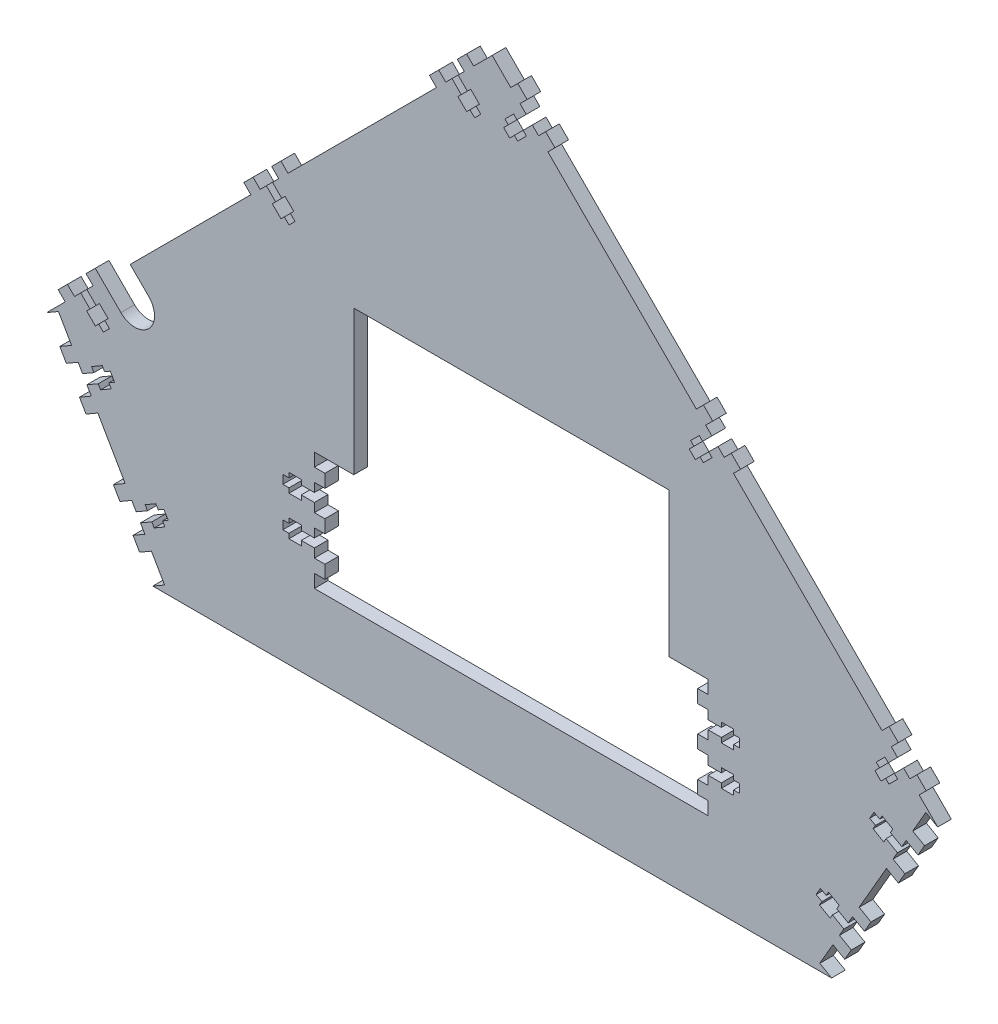
SolidWorks part; units mm, degrees
material "Acrylic (Blue)"
ref_plane "Front Plane" through (0, 0, 0) normal (0, 0, 1) x (1, 0, 0)
ref_plane "Top Plane" through (0, 0, 0) normal (0, 1, 0) x (1, 0, 0)
ref_plane "Right Plane" through (0, 0, 0) normal (1, 0, 0) x (0, 0, -1)
sketch "Sketch1" plane through (0, 0, 0) normal (0, 0, 1) x (1, 0, 0)
  line L0 (0, 0) -> (0, 304.4261) construction
  line L1 (0, 304.4261) -> (215.5261, 88.9)
  line L2 (215.5261, 88.9) -> (164.1997, 0)
  line L3 (164.1997, 0) -> (0, 0)
  line L4 (0, 304.4261) -> (-215.5261, 88.9)
  line L5 (-215.5261, 88.9) -> (-164.1997, 0)
  line L6 (-164.1997, 0) -> (0, 0)
  line L7 (-215.5261, 88.9) -> (215.5261, 88.9) construction
  line L8 (0, 304.4261) -> (3.5921, 308.0182) construction
  line L9 (3.5921, 308.0182) -> (219.1182, 92.4921) construction
  line L10 (219.1182, 92.4921) -> (215.5261, 88.9) construction
  line L11 (3.5921, 308.0182) -> (0, 311.6104) construction
  line L12 (0, 311.6104) -> (-219.1182, 92.4921) construction
  line L13 (-219.1182, 92.4921) -> (-215.5261, 88.9) construction
  line L14 (215.5261, 88.9) -> (219.9256, 86.36) construction
  line L15 (219.9256, 86.36) -> (168.5991, -2.54) construction
  line L16 (168.5991, -2.54) -> (164.1997, 0) construction
  line L17 (164.1997, 0) -> (164.1997, -12.7) construction
  line L18 (164.1997, -12.7) -> (-164.1997, -12.7) construction
  line L19 (-164.1997, -12.7) -> (-164.1997, 0) construction
  line L20 (-164.1997, 0) -> (-168.5991, -2.54) construction
  line L21 (-168.5991, -2.54) -> (-219.9256, 86.36) construction
  line L22 (-219.9256, 86.36) -> (-215.5261, 88.9) construction
  dimension "D1" = 304.8
  dimension "D2" = 120
  dimension "D3" = 88.9
  dimension "D4" = 5.08
  dimension "D5" = 12.7
extrude "Boss-Extrude1" add sketch "Sketch1" along normal blind 6.604
sketch "Sketch2" plane through (0, 0, 6.604) normal (0, 0, 1) x (1, 0, 0)
  line L0 (215.5261, 88.9) -> (0, 304.4261) construction
  line L1 (-66.9554, 165.1) -> (85.4446, 165.1)
  line L2 (-66.9554, 38.1) -> (85.4446, 38.1)
  line L3 (85.4446, 165.1) -> (85.4446, 95.25)
  line L4 (-66.9554, 165.1) -> (-66.9554, 95.25)
  line L6 (-164.1997, 0) -> (164.1997, 0) construction
  line L7 (-66.9554, 38.1) -> (-86.0054, 38.1)
  line L9 (-66.9554, 95.25) -> (-86.0054, 95.25)
  line L10 (-86.0054, 38.1) -> (-86.0054, 95.25)
  line L11 (85.4446, 38.1) -> (104.4946, 38.1)
  line L13 (85.4446, 95.25) -> (104.4946, 95.25)
  line L14 (104.4946, 38.1) -> (104.4946, 95.25)
  dimension "D1" = 127
  dimension "D2" = 38.1
  dimension "D3" = 38.1
  dimension "D4" = 152.4
  dimension "D5" = 19.05
  dimension "D6" = 57.15
extrude "Cut-Extrude1" cut sketch "Sketch2" against normal through all
sketch "Sketch3" plane through (0, 0, 6.604) normal (0, 0, 1) x (1, 0, 0)
  line L0 (-209.8069, 92.202) -> (-215.5261, 88.9)
  line L1 (-215.5261, 88.9) -> (-164.1997, 0)
  line L2 (-164.1997, 0) -> (-158.4805, 3.302)
  line L3 (-158.4805, 3.302) -> (-209.8069, 92.202)
  line L4 (0, 304.4261) -> (0, 0) construction
  line L5 (158.4805, 3.302) -> (209.8069, 92.202)
  line L6 (164.1997, 0) -> (158.4805, 3.302)
  line L7 (215.5261, 88.9) -> (164.1997, 0)
  line L8 (209.8069, 92.202) -> (215.5261, 88.9)
  dimension "D1" = 6.604
extrude "Cut-Extrude2" cut sketch "Sketch3" against normal through all
sketch "Sketch4" plane through (0, 0, 6.604) normal (0, 0, 1) x (1, 0, 0)
  line L0 (0, 304.4261) -> (-215.5261, 88.9) construction
  line L1 (-30.3533, 280.8979) -> (-102.1953, 209.0558) construction
  line L3 (-120.1558, 191.0953) -> (-191.9979, 119.2533) construction
  line L4 (215.5261, 88.9) -> (0, 304.4261) construction
  line L5 (120.1558, 191.0953) -> (191.9979, 119.2533) construction
  line L6 (30.3533, 280.8979) -> (102.1953, 209.0558) construction
  line L7 (215.5261, 88.9) -> (209.8069, 92.202) construction
  line L8 (-158.4805, 3.302) -> (-209.8069, 92.202) construction
  line L9 (-209.8069, 92.202) -> (-215.5261, 88.9) construction
  line L11 (158.4805, 3.302) -> (164.1997, 0) construction
  line L13 (-164.1997, 0) -> (-158.4805, 3.302) construction
  line L14 (209.8069, 92.202) -> (158.4805, 3.302) construction
  line L15 (104.4946, 38.1) -> (104.4946, 95.25) construction
  line L16 (-86.0054, 95.25) -> (-86.0054, 38.1) construction
  line L17 (104.4946, 95.25) -> (85.4446, 95.25) construction
  line B0 (-19.4333, 284.9929) -> (-14.9431, 280.5027) construction
  line B1 (-14.9431, 280.5027) -> (-16.5596, 278.8863) construction
  line B2 (-16.5596, 278.8863) -> (-12.3568, 274.6835) construction
  line B3 (-12.3568, 274.6835) -> (-10.7404, 276.3) construction
  line B4 (-10.7404, 276.3) -> (-8.4774, 274.037) construction
  line B5 (-8.4774, 274.037) -> (-5.5318, 276.9825) construction
  line B6 (-5.5318, 276.9825) -> (-7.7949, 279.2455) construction
  line B7 (-7.7949, 279.2455) -> (-6.1784, 280.862) construction
  line B8 (-6.1784, 280.862) -> (-10.3812, 285.0647) construction
  line B9 (-10.3812, 285.0647) -> (-11.9976, 283.4483) construction
  line B10 (-11.9976, 283.4483) -> (-16.4878, 287.9384) construction
  line B11 (-13.4704, 290.9558) -> (-16.8829, 294.3683) construction
  line B12 (-16.8829, 294.3683) -> (-12.3928, 298.8584) construction
  line B13 (-12.3928, 298.8584) -> (-8.9803, 295.4459) construction
  line B14 (-19.4333, 284.9929) -> (-22.4506, 281.9755) construction
  line B15 (-22.4506, 281.9755) -> (-25.8631, 285.388) construction
  line B16 (-25.8631, 285.388) -> (-30.3533, 280.8979) construction
  line B17 (-30.3533, 280.8979) -> (-26.9408, 277.4854) construction
  line B18 (-16.4878, 287.9384) -> (-19.4333, 284.9929) construction
  line B19 (-109.2358, 195.1903) -> (-104.7457, 190.7002) construction
  line B20 (-104.7457, 190.7002) -> (-106.3622, 189.0837) construction
  line B21 (-106.3622, 189.0837) -> (-102.1594, 184.881) construction
  line B22 (-102.1594, 184.881) -> (-100.5429, 186.4974) construction
  line B23 (-100.5429, 186.4974) -> (-98.2799, 184.2344) construction
  line B24 (-98.2799, 184.2344) -> (-95.3344, 187.1799) construction
  line B25 (-95.3344, 187.1799) -> (-97.5974, 189.4429) construction
  line B26 (-97.5974, 189.4429) -> (-95.981, 191.0594) construction
  line B27 (-95.981, 191.0594) -> (-100.1837, 195.2622) construction
  line B28 (-100.1837, 195.2622) -> (-101.8002, 193.6457) construction
  line B29 (-101.8002, 193.6457) -> (-106.2903, 198.1358) construction
  line B30 (-103.2729, 201.1532) -> (-106.6854, 204.5657) construction
  line B31 (-106.6854, 204.5657) -> (-102.1953, 209.0558) construction
  line B32 (-102.1953, 209.0558) -> (-98.7828, 205.6433) construction
  line B33 (-112.2532, 192.1729) -> (-115.6657, 195.5854) construction
  line B34 (-115.6657, 195.5854) -> (-120.1558, 191.0953) construction
  line B35 (-120.1558, 191.0953) -> (-116.7433, 187.6828) construction
  line B36 (-106.2903, 198.1358) -> (-109.2358, 195.1903) construction
  line B37 (-199.0384, 105.3878) -> (-194.5483, 100.8976) construction
  line B38 (-194.5483, 100.8976) -> (-196.1647, 99.2812) construction
  line B39 (-196.1647, 99.2812) -> (-191.962, 95.0784) construction
  line B40 (-191.962, 95.0784) -> (-190.3455, 96.6949) construction
  line B41 (-190.3455, 96.6949) -> (-188.0825, 94.4318) construction
  line B42 (-188.0825, 94.4318) -> (-185.137, 97.3774) construction
  line B43 (-185.137, 97.3774) -> (-187.4, 99.6404) construction
  line B44 (-187.4, 99.6404) -> (-185.7835, 101.2568) construction
  line B45 (-185.7835, 101.2568) -> (-189.9863, 105.4596) construction
  line B46 (-189.9863, 105.4596) -> (-191.6027, 103.8431) construction
  line B47 (-191.6027, 103.8431) -> (-196.0929, 108.3333) construction
  line B48 (-196.0929, 108.3333) -> (-193.0755, 111.3506) construction
  line B49 (-193.0755, 111.3506) -> (-196.488, 114.7631) construction
  line B50 (-196.488, 114.7631) -> (-191.9979, 119.2533) construction
  line B51 (-191.9979, 119.2533) -> (-188.5854, 115.8408) construction
  line B52 (-199.0384, 105.3878) -> (-202.0558, 102.3704) construction
  line B53 (-202.0558, 102.3704) -> (-205.4683, 105.7829) construction
  line B54 (-205.4683, 105.7829) -> (-209.9584, 101.2928) construction
  line B55 (-209.9584, 101.2928) -> (-206.5459, 97.8803) construction
  line B56 (-196.0929, 108.3333) -> (-199.0384, 105.3878) construction
  line B57 (16.4878, 287.9384) -> (11.9976, 283.4483) construction
  line B58 (11.9976, 283.4483) -> (10.3812, 285.0647) construction
  line B59 (10.3812, 285.0647) -> (6.1784, 280.862) construction
  line B60 (6.1784, 280.862) -> (7.7949, 279.2455) construction
  line B61 (7.7949, 279.2455) -> (5.5318, 276.9825) construction
  line B62 (5.5318, 276.9825) -> (8.4774, 274.037) construction
  line B63 (8.4774, 274.037) -> (10.7404, 276.3) construction
  line B64 (10.7404, 276.3) -> (12.3568, 274.6835) construction
  line B65 (12.3568, 274.6835) -> (16.5596, 278.8863) construction
  line B66 (16.5596, 278.8863) -> (14.9431, 280.5027) construction
  line B67 (14.9431, 280.5027) -> (19.4333, 284.9929) construction
  line B68 (19.4333, 284.9929) -> (22.4506, 281.9755) construction
  line B69 (22.4506, 281.9755) -> (25.8631, 285.388) construction
  line B70 (25.8631, 285.388) -> (30.3533, 280.8979) construction
  line B71 (30.3533, 280.8979) -> (26.9408, 277.4854) construction
  line B72 (16.4878, 287.9384) -> (13.4704, 290.9558) construction
  line B73 (13.4704, 290.9558) -> (16.8829, 294.3683) construction
  line B74 (16.8829, 294.3683) -> (12.3928, 298.8584) construction
  line B75 (12.3928, 298.8584) -> (8.9803, 295.4459) construction
  line B76 (19.4333, 284.9929) -> (16.4878, 287.9384) construction
  line B77 (106.2903, 198.1358) -> (101.8002, 193.6457) construction
  line B78 (101.8002, 193.6457) -> (100.1837, 195.2622) construction
  line B79 (100.1837, 195.2622) -> (95.981, 191.0594) construction
  line B80 (95.981, 191.0594) -> (97.5974, 189.4429) construction
  line B81 (97.5974, 189.4429) -> (95.3344, 187.1799) construction
  line B82 (95.3344, 187.1799) -> (98.2799, 184.2344) construction
  line B83 (98.2799, 184.2344) -> (100.5429, 186.4974) construction
  line B84 (100.5429, 186.4974) -> (102.1594, 184.881) construction
  line B85 (102.1594, 184.881) -> (106.3622, 189.0837) construction
  line B86 (106.3622, 189.0837) -> (104.7457, 190.7002) construction
  line B87 (104.7457, 190.7002) -> (109.2358, 195.1903) construction
  line B88 (109.2358, 195.1903) -> (112.2532, 192.1729) construction
  line B89 (112.2532, 192.1729) -> (115.6657, 195.5854) construction
  line B90 (115.6657, 195.5854) -> (120.1558, 191.0953) construction
  line B91 (120.1558, 191.0953) -> (116.7433, 187.6828) construction
  line B92 (106.2903, 198.1358) -> (103.2729, 201.1532) construction
  line B93 (103.2729, 201.1532) -> (106.6854, 204.5657) construction
  line B94 (106.6854, 204.5657) -> (102.1953, 209.0558) construction
  line B95 (102.1953, 209.0558) -> (98.7828, 205.6433) construction
  line B96 (109.2358, 195.1903) -> (106.2903, 198.1358) construction
  line B97 (196.0929, 108.3333) -> (191.6027, 103.8431) construction
  line B98 (191.6027, 103.8431) -> (189.9863, 105.4596) construction
  line B99 (189.9863, 105.4596) -> (185.7835, 101.2568) construction
  line B100 (185.7835, 101.2568) -> (187.4, 99.6404) construction
  line B101 (187.4, 99.6404) -> (185.137, 97.3774) construction
  line B102 (185.137, 97.3774) -> (188.0825, 94.4318) construction
  line B103 (188.0825, 94.4318) -> (190.3455, 96.6949) construction
  line B104 (190.3455, 96.6949) -> (191.962, 95.0784) construction
  line B105 (191.962, 95.0784) -> (196.1647, 99.2812) construction
  line B106 (196.1647, 99.2812) -> (194.5483, 100.8976) construction
  line B107 (194.5483, 100.8976) -> (199.0384, 105.3878) construction
  line B108 (199.0384, 105.3878) -> (202.0558, 102.3704) construction
  line B109 (202.0558, 102.3704) -> (205.4683, 105.7829) construction
  line B110 (205.4683, 105.7829) -> (209.9584, 101.2928) construction
  line B111 (209.9584, 101.2928) -> (206.5459, 97.8803) construction
  line B112 (193.0755, 111.3506) -> (196.488, 114.7631) construction
  line B113 (196.488, 114.7631) -> (191.9979, 119.2533) construction
  line B114 (191.9979, 119.2533) -> (188.5854, 115.8408) construction
  line B115 (199.0384, 105.3878) -> (196.0929, 108.3333) construction
  line B116 (198.1483, 72.0087) -> (192.6491, 75.1837) construction
  line B117 (192.6491, 75.1837) -> (193.7921, 77.1634) construction
  line B118 (193.7921, 77.1634) -> (188.6447, 80.1352) construction
  line B119 (188.6447, 80.1352) -> (187.5017, 78.1555) construction
  line B120 (187.5017, 78.1555) -> (184.7301, 79.7557) construction
  line B121 (184.7301, 79.7557) -> (182.6473, 76.1482) construction
  line B122 (182.6473, 76.1482) -> (185.4189, 74.548) construction
  line B123 (185.4189, 74.548) -> (184.2759, 72.5683) construction
  line B124 (184.2759, 72.5683) -> (189.4233, 69.5965) construction
  line B125 (189.4233, 69.5965) -> (190.5663, 71.5762) construction
  line B126 (190.5663, 71.5762) -> (196.0655, 68.4012) construction
  line B127 (196.0655, 68.4012) -> (193.9319, 64.7057) construction
  line B128 (193.9319, 64.7057) -> (198.1114, 62.2927) construction
  line B129 (198.1114, 62.2927) -> (194.9364, 56.7934) construction
  line B130 (194.9364, 56.7934) -> (190.7569, 59.2064) construction
  line B131 (198.1483, 72.0087) -> (200.2819, 75.7042) construction
  line B132 (200.2819, 75.7042) -> (204.4614, 73.2912) construction
  line B133 (204.4614, 73.2912) -> (207.6364, 78.7905) construction
  line B134 (207.6364, 78.7905) -> (203.4569, 81.2035) construction
  line B135 (196.0655, 68.4012) -> (198.1483, 72.0087) construction
  line B136 (172.2219, 27.1028) -> (166.7226, 30.2778) construction
  line B137 (166.7226, 30.2778) -> (167.8656, 32.2575) construction
  line B138 (167.8656, 32.2575) -> (162.7183, 35.2293) construction
  line B139 (162.7183, 35.2293) -> (161.5753, 33.2496) construction
  line B140 (161.5753, 33.2496) -> (158.8037, 34.8498) construction
  line B141 (158.8037, 34.8498) -> (156.7209, 31.2423) construction
  line B142 (156.7209, 31.2423) -> (159.4925, 29.6421) construction
  line B143 (159.4925, 29.6421) -> (158.3495, 27.6624) construction
  line B144 (158.3495, 27.6624) -> (163.4968, 24.6906) construction
  line B145 (163.4968, 24.6906) -> (164.6398, 26.6703) construction
  line B146 (164.6398, 26.6703) -> (170.1391, 23.4953) construction
  line B147 (170.1391, 23.4953) -> (168.0055, 19.7998) construction
  line B148 (168.0055, 19.7998) -> (172.1849, 17.3868) construction
  line B149 (172.1849, 17.3868) -> (169.0099, 11.8875) construction
  line B150 (169.0099, 11.8875) -> (164.8305, 14.3005) construction
  line B151 (172.2219, 27.1028) -> (174.3555, 30.7983) construction
  line B152 (174.3555, 30.7983) -> (178.5349, 28.3853) construction
  line B153 (178.5349, 28.3853) -> (181.7099, 33.8846) construction
  line B154 (181.7099, 33.8846) -> (177.5305, 36.2976) construction
  line B155 (170.1391, 23.4953) -> (172.2219, 27.1028) construction
  line B156 (-170.1391, 23.4953) -> (-164.6398, 26.6703) construction
  line B157 (-164.6398, 26.6703) -> (-163.4968, 24.6906) construction
  line B158 (-163.4968, 24.6906) -> (-158.3495, 27.6624) construction
  line B159 (-158.3495, 27.6624) -> (-159.4925, 29.6421) construction
  line B160 (-159.4925, 29.6421) -> (-156.7209, 31.2423) construction
  line B161 (-156.7209, 31.2423) -> (-158.8037, 34.8498) construction
  line B162 (-158.8037, 34.8498) -> (-161.5753, 33.2496) construction
  line B163 (-161.5753, 33.2496) -> (-162.7183, 35.2293) construction
  line B164 (-162.7183, 35.2293) -> (-167.8656, 32.2575) construction
  line B165 (-167.8656, 32.2575) -> (-166.7226, 30.2778) construction
  line B166 (-166.7226, 30.2778) -> (-172.2219, 27.1028) construction
  line B167 (-172.2219, 27.1028) -> (-174.3555, 30.7983) construction
  line B168 (-174.3555, 30.7983) -> (-178.5349, 28.3853) construction
  line B169 (-178.5349, 28.3853) -> (-181.7099, 33.8846) construction
  line B170 (-181.7099, 33.8846) -> (-177.5305, 36.2976) construction
  line B171 (-168.0055, 19.7998) -> (-172.1849, 17.3868) construction
  line B172 (-172.1849, 17.3868) -> (-169.0099, 11.8875) construction
  line B173 (-169.0099, 11.8875) -> (-164.8305, 14.3005) construction
  line B174 (-172.2219, 27.1028) -> (-170.1391, 23.4953) construction
  line B175 (-196.0655, 68.4012) -> (-190.5663, 71.5762) construction
  line B176 (-190.5663, 71.5762) -> (-189.4233, 69.5965) construction
  line B177 (-189.4233, 69.5965) -> (-184.2759, 72.5683) construction
  line B178 (-184.2759, 72.5683) -> (-185.4189, 74.548) construction
  line B179 (-185.4189, 74.548) -> (-182.6473, 76.1482) construction
  line B180 (-182.6473, 76.1482) -> (-184.7301, 79.7557) construction
  line B181 (-184.7301, 79.7557) -> (-187.5017, 78.1555) construction
  line B182 (-187.5017, 78.1555) -> (-188.6447, 80.1352) construction
  line B183 (-188.6447, 80.1352) -> (-193.7921, 77.1634) construction
  line B184 (-193.7921, 77.1634) -> (-192.6491, 75.1837) construction
  line B185 (-192.6491, 75.1837) -> (-198.1483, 72.0087) construction
  line B186 (-200.2819, 75.7042) -> (-204.4614, 73.2912) construction
  line B187 (-204.4614, 73.2912) -> (-207.6364, 78.7905) construction
  line B188 (-207.6364, 78.7905) -> (-203.4569, 81.2035) construction
  line B189 (-196.0655, 68.4012) -> (-193.9319, 64.7057) construction
  line B190 (-193.9319, 64.7057) -> (-198.1114, 62.2927) construction
  line B191 (-198.1114, 62.2927) -> (-194.9364, 56.7934) construction
  line B192 (-194.9364, 56.7934) -> (-190.7569, 59.2064) construction
  line B193 (-198.1483, 72.0087) -> (-196.0655, 68.4012) construction
  line B194 (-86.0054, 78.2828) -> (-92.3554, 78.2828)
  line B195 (-92.3554, 78.2828) -> (-92.3554, 80.5688)
  line B196 (-92.3554, 80.5688) -> (-98.299, 80.5688)
  line B197 (-98.299, 80.5688) -> (-98.299, 78.2828)
  line B198 (-98.299, 78.2828) -> (-101.2454, 78.2828)
  line B199 (-101.2454, 78.2828) -> (-101.2454, 74.1172)
  line B200 (-101.2454, 74.1172) -> (-98.299, 74.1172)
  line B201 (-98.299, 74.1172) -> (-98.299, 71.8312)
  line B202 (-98.299, 71.8312) -> (-92.3554, 71.8312)
  line B203 (-92.3554, 71.8312) -> (-92.3554, 74.1172)
  line B204 (-92.3554, 74.1172) -> (-86.0054, 74.1172)
  line B205 (-86.0054, 74.1172) -> (-86.0054, 69.85)
  line B206 (-86.0054, 69.85) -> (-80.9254, 69.85)
  line B207 (-80.9254, 69.85) -> (-80.9254, 63.5)
  line B208 (-80.9254, 63.5) -> (-86.0054, 63.5)
  line B209 (-86.0054, 78.2828) -> (-86.0054, 82.55)
  line B210 (-86.0054, 82.55) -> (-80.9254, 82.55)
  line B211 (-80.9254, 82.55) -> (-80.9254, 88.9)
  line B212 (-80.9254, 88.9) -> (-86.0054, 88.9)
  line B213 (-86.0054, 74.1172) -> (-86.0054, 78.2828) construction
  line B214 (-80.9254, 44.45) -> (-86.0054, 44.45)
  line B215 (-86.0054, 59.2328) -> (-92.3554, 59.2328)
  line B216 (-92.3554, 59.2328) -> (-92.3554, 61.5188)
  line B217 (-92.3554, 61.5188) -> (-98.299, 61.5188)
  line B218 (-98.299, 61.5188) -> (-98.299, 59.2328)
  line B219 (-98.299, 59.2328) -> (-101.2454, 59.2328)
  line B220 (-101.2454, 59.2328) -> (-101.2454, 55.0672)
  line B221 (-101.2454, 55.0672) -> (-98.299, 55.0672)
  line B222 (-98.299, 55.0672) -> (-98.299, 52.7812)
  line B223 (-98.299, 52.7812) -> (-92.3554, 52.7812)
  line B224 (-92.3554, 52.7812) -> (-92.3554, 55.0672)
  line B225 (-92.3554, 55.0672) -> (-86.0054, 55.0672)
  line B226 (-86.0054, 55.0672) -> (-86.0054, 50.8)
  line B227 (-86.0054, 50.8) -> (-80.9254, 50.8)
  line B228 (-80.9254, 50.8) -> (-80.9254, 44.45)
  line B229 (-86.0054, 59.2328) -> (-86.0054, 63.5)
  line B230 (-86.0054, 55.0672) -> (-86.0054, 59.2328) construction
  line B231 (104.4946, 55.0672) -> (110.8446, 55.0672)
  line B232 (110.8446, 55.0672) -> (110.8446, 52.7812)
  line B233 (110.8446, 52.7812) -> (116.7882, 52.7812)
  line B234 (116.7882, 52.7812) -> (116.7882, 55.0672)
  line B235 (116.7882, 55.0672) -> (119.7346, 55.0672)
  line B236 (119.7346, 55.0672) -> (119.7346, 59.2328)
  line B237 (119.7346, 59.2328) -> (116.7882, 59.2328)
  line B238 (116.7882, 59.2328) -> (116.7882, 61.5188)
  line B239 (116.7882, 61.5188) -> (110.8446, 61.5188)
  line B240 (110.8446, 61.5188) -> (110.8446, 59.2328)
  line B241 (110.8446, 59.2328) -> (104.4946, 59.2328)
  line B242 (104.4946, 59.2328) -> (104.4946, 63.5)
  line B243 (104.4946, 63.5) -> (99.4146, 63.5)
  line B244 (99.4146, 63.5) -> (99.4146, 69.85)
  line B245 (99.4146, 69.85) -> (104.4946, 69.85)
  line B246 (104.4946, 50.8) -> (99.4146, 50.8)
  line B247 (99.4146, 50.8) -> (99.4146, 44.45)
  line B248 (99.4146, 44.45) -> (104.4946, 44.45)
  line B249 (104.4946, 59.2328) -> (104.4946, 55.0672) construction
  line B250 (99.4146, 88.9) -> (104.4946, 88.9)
  line B251 (104.4946, 74.1172) -> (110.8446, 74.1172)
  line B252 (110.8446, 74.1172) -> (110.8446, 71.8312)
  line B253 (110.8446, 71.8312) -> (116.7882, 71.8312)
  line B254 (116.7882, 71.8312) -> (116.7882, 74.1172)
  line B255 (116.7882, 74.1172) -> (119.7346, 74.1172)
  line B256 (119.7346, 74.1172) -> (119.7346, 78.2828)
  line B257 (119.7346, 78.2828) -> (116.7882, 78.2828)
  line B258 (116.7882, 78.2828) -> (116.7882, 80.5688)
  line B259 (116.7882, 80.5688) -> (110.8446, 80.5688)
  line B260 (110.8446, 80.5688) -> (110.8446, 78.2828)
  line B261 (110.8446, 78.2828) -> (104.4946, 78.2828)
  line B262 (104.4946, 78.2828) -> (104.4946, 82.55)
  line B263 (104.4946, 82.55) -> (99.4146, 82.55)
  line B264 (99.4146, 82.55) -> (99.4146, 88.9)
  line B265 (104.4946, 74.1172) -> (104.4946, 69.85)
  line B266 (104.4946, 78.2828) -> (104.4946, 74.1172) construction
  dimension "D1" = 12.7
  dimension "D2" = 12.7
  dimension "D3" = 12.7
  dimension "D4" = 12.7
  dimension "D5" = 12.7
  dimension "D6" = 12.7
  dimension "D7" = 12.7
  dimension "D8" = 12.7
  dimension "D9" = 6.35
sketch_block_instance "NUT_HOLE-1"
sketch_block "NUT_HOLE" parameters "D1"=6.35, "D2"=4.1656, "D3"=25.4, "D4"=4.826, "D5"=8.7376, "D6"=5.9436, "D7"=6.35, "D8"=20.32
sketch_block_instance "NUT_HOLE-2"
sketch_block_instance "NUT_HOLE-3"
sketch_block_instance "NUT_HOLE-4"
sketch_block_instance "NUT_HOLE-5"
sketch_block_instance "NUT_HOLE-6"
sketch_block_instance "NUT_HOLE-7"
sketch_block_instance "NUT_HOLE-8"
sketch_block_instance "NUT_HOLE-9"
sketch_block_instance "NUT_HOLE-10"
sketch_block_instance "NUT_HOLE_2X-1"
sketch_block "NUT_HOLE_2X" parameters "D1"=6.35, "D2"=4.1656, "D3"=25.4, "D4"=5.08, "D5"=8.7376, "D6"=5.9436, "D7"=6.35, "D8"=20.32, "D9"=2
sketch_block_instance "NUT_HOLE_2X-2"
sketch "Sketch6" plane through (0, 0, 6.604) normal (0, 0, 1) x (1, 0, 0)
  line L0 (-11.9976, 283.4483) -> (-16.4878, 287.9384) construction
  line L1 (-10.3812, 285.0647) -> (-11.9976, 283.4483) construction
  line L2 (-6.1784, 280.862) -> (-10.3812, 285.0647) construction
  line L3 (-19.4333, 284.9929) -> (-14.9431, 280.5027) construction
  line L4 (-14.9431, 280.5027) -> (-16.5596, 278.8863) construction
  line L5 (-16.5596, 278.8863) -> (-12.3568, 274.6835) construction
  line L6 (-12.3568, 274.6835) -> (-10.7404, 276.3) construction
  line L7 (-10.7404, 276.3) -> (-8.4774, 274.037) construction
  line L8 (-5.5318, 276.9825) -> (-7.7949, 279.2455) construction
  line L9 (-7.7949, 279.2455) -> (-6.1784, 280.862) construction
  line L10 (-8.4774, 274.037) -> (-5.5318, 276.9825) construction
  line L11 (-101.8002, 193.6457) -> (-106.2903, 198.1358) construction
  line L12 (-100.1837, 195.2622) -> (-101.8002, 193.6457) construction
  line L13 (-95.981, 191.0594) -> (-100.1837, 195.2622) construction
  line L14 (-97.5974, 189.4429) -> (-95.981, 191.0594) construction
  line L15 (-95.3344, 187.1799) -> (-97.5974, 189.4429) construction
  line L16 (-98.2799, 184.2344) -> (-95.3344, 187.1799) construction
  line L17 (-100.5429, 186.4974) -> (-98.2799, 184.2344) construction
  line L18 (-102.1594, 184.881) -> (-100.5429, 186.4974) construction
  line L19 (-106.3622, 189.0837) -> (-102.1594, 184.881) construction
  line L20 (-104.7457, 190.7002) -> (-106.3622, 189.0837) construction
  line L21 (-109.2358, 195.1903) -> (-104.7457, 190.7002) construction
  line L22 (-199.0384, 105.3878) -> (-194.5483, 100.8976) construction
  line L23 (-191.6027, 103.8431) -> (-196.0929, 108.3333) construction
  line L24 (-194.5483, 100.8976) -> (-196.1647, 99.2812) construction
  line L25 (-196.1647, 99.2812) -> (-191.962, 95.0784) construction
  line L26 (-191.962, 95.0784) -> (-190.3455, 96.6949) construction
  line L27 (-190.3455, 96.6949) -> (-188.0825, 94.4318) construction
  line L28 (-188.0825, 94.4318) -> (-185.137, 97.3774) construction
  line L29 (-185.137, 97.3774) -> (-187.4, 99.6404) construction
  line L30 (-187.4, 99.6404) -> (-185.7835, 101.2568) construction
  line L31 (-189.9863, 105.4596) -> (-191.6027, 103.8431) construction
  line L32 (-185.7835, 101.2568) -> (-189.9863, 105.4596) construction
  line L33 (-192.6491, 75.1837) -> (-198.1483, 72.0087) construction
  line L34 (-193.7921, 77.1634) -> (-192.6491, 75.1837) construction
  line L35 (-188.6447, 80.1352) -> (-193.7921, 77.1634) construction
  line L36 (-187.5017, 78.1555) -> (-188.6447, 80.1352) construction
  line L37 (-184.7301, 79.7557) -> (-187.5017, 78.1555) construction
  line L38 (-182.6473, 76.1482) -> (-184.7301, 79.7557) construction
  line L39 (-185.4189, 74.548) -> (-182.6473, 76.1482) construction
  line L40 (-189.4233, 69.5965) -> (-184.2759, 72.5683) construction
  line L41 (-184.2759, 72.5683) -> (-185.4189, 74.548) construction
  line L42 (-196.0655, 68.4012) -> (-190.5663, 71.5762) construction
  line L43 (-190.5663, 71.5762) -> (-189.4233, 69.5965) construction
  line L44 (-166.7226, 30.2778) -> (-172.2219, 27.1028) construction
  line L45 (-167.8656, 32.2575) -> (-166.7226, 30.2778) construction
  line L46 (-162.7183, 35.2293) -> (-167.8656, 32.2575) construction
  line L47 (-161.5753, 33.2496) -> (-162.7183, 35.2293) construction
  line L48 (-158.8037, 34.8498) -> (-161.5753, 33.2496) construction
  line L49 (-156.7209, 31.2423) -> (-158.8037, 34.8498) construction
  line L50 (-159.4925, 29.6421) -> (-156.7209, 31.2423) construction
  line L51 (-158.3495, 27.6624) -> (-159.4925, 29.6421) construction
  line L52 (-163.4968, 24.6906) -> (-158.3495, 27.6624) construction
  line L53 (-164.6398, 26.6703) -> (-163.4968, 24.6906) construction
  line L54 (-170.1391, 23.4953) -> (-164.6398, 26.6703) construction
  line L55 (10.3812, 285.0647) -> (6.1784, 280.862) construction
  line L56 (11.9976, 283.4483) -> (10.3812, 285.0647) construction
  line L57 (16.4878, 287.9384) -> (11.9976, 283.4483) construction
  line L58 (14.9431, 280.5027) -> (19.4333, 284.9929) construction
  line L59 (16.5596, 278.8863) -> (14.9431, 280.5027) construction
  line L60 (12.3568, 274.6835) -> (16.5596, 278.8863) construction
  line L61 (10.7404, 276.3) -> (12.3568, 274.6835) construction
  line L62 (8.4774, 274.037) -> (10.7404, 276.3) construction
  line L63 (5.5318, 276.9825) -> (8.4774, 274.037) construction
  line L64 (7.7949, 279.2455) -> (5.5318, 276.9825) construction
  line L65 (6.1784, 280.862) -> (7.7949, 279.2455) construction
  line L66 (106.2903, 198.1358) -> (101.8002, 193.6457) construction
  line L67 (101.8002, 193.6457) -> (100.1837, 195.2622) construction
  line L68 (100.1837, 195.2622) -> (95.981, 191.0594) construction
  line L69 (95.981, 191.0594) -> (97.5974, 189.4429) construction
  line L70 (97.5974, 189.4429) -> (95.3344, 187.1799) construction
  line L71 (95.3344, 187.1799) -> (98.2799, 184.2344) construction
  line L72 (98.2799, 184.2344) -> (100.5429, 186.4974) construction
  line L73 (100.5429, 186.4974) -> (102.1594, 184.881) construction
  line L74 (102.1594, 184.881) -> (106.3622, 189.0837) construction
  line L75 (104.7457, 190.7002) -> (109.2358, 195.1903) construction
  line L76 (106.3622, 189.0837) -> (104.7457, 190.7002) construction
  line L77 (194.5483, 100.8976) -> (199.0384, 105.3878) construction
  line L78 (196.0929, 108.3333) -> (191.6027, 103.8431) construction
  line L79 (189.9863, 105.4596) -> (185.7835, 101.2568) construction
  line L80 (191.6027, 103.8431) -> (189.9863, 105.4596) construction
  line L81 (185.7835, 101.2568) -> (187.4, 99.6404) construction
  line L82 (187.4, 99.6404) -> (185.137, 97.3774) construction
  line L83 (185.137, 97.3774) -> (188.0825, 94.4318) construction
  line L84 (188.0825, 94.4318) -> (190.3455, 96.6949) construction
  line L85 (190.3455, 96.6949) -> (191.962, 95.0784) construction
  line L86 (191.962, 95.0784) -> (196.1647, 99.2812) construction
  line L87 (196.1647, 99.2812) -> (194.5483, 100.8976) construction
  line L88 (188.6447, 80.1352) -> (187.5017, 78.1555) construction
  line L89 (187.5017, 78.1555) -> (184.7301, 79.7557) construction
  line L90 (184.7301, 79.7557) -> (182.6473, 76.1482) construction
  line L91 (182.6473, 76.1482) -> (185.4189, 74.548) construction
  line L92 (185.4189, 74.548) -> (184.2759, 72.5683) construction
  line L93 (184.2759, 72.5683) -> (189.4233, 69.5965) construction
  line L94 (193.7921, 77.1634) -> (188.6447, 80.1352) construction
  line L95 (192.6491, 75.1837) -> (193.7921, 77.1634) construction
  line L96 (198.1483, 72.0087) -> (192.6491, 75.1837) construction
  line L97 (190.5663, 71.5762) -> (196.0655, 68.4012) construction
  line L98 (189.4233, 69.5965) -> (190.5663, 71.5762) construction
  line L99 (161.5753, 33.2496) -> (158.8037, 34.8498) construction
  line L100 (158.8037, 34.8498) -> (156.7209, 31.2423) construction
  line L101 (162.7183, 35.2293) -> (161.5753, 33.2496) construction
  line L102 (167.8656, 32.2575) -> (162.7183, 35.2293) construction
  line L103 (166.7226, 30.2778) -> (167.8656, 32.2575) construction
  line L104 (172.2219, 27.1028) -> (166.7226, 30.2778) construction
  line L105 (164.6398, 26.6703) -> (170.1391, 23.4953) construction
  line L106 (163.4968, 24.6906) -> (164.6398, 26.6703) construction
  line L107 (156.7209, 31.2423) -> (159.4925, 29.6421) construction
  line L108 (159.4925, 29.6421) -> (158.3495, 27.6624) construction
  line L109 (158.3495, 27.6624) -> (163.4968, 24.6906) construction
  line L110 (-11.9976, 283.4483) -> (-16.4878, 287.9384)
  line L111 (-10.3812, 285.0647) -> (-11.9976, 283.4483)
  line L112 (-6.1784, 280.862) -> (-10.3812, 285.0647)
  line L113 (-19.4333, 284.9929) -> (-14.9431, 280.5027)
  line L114 (-14.9431, 280.5027) -> (-16.5596, 278.8863)
  line L115 (-16.5596, 278.8863) -> (-12.3568, 274.6835)
  line L116 (-12.3568, 274.6835) -> (-10.7404, 276.3)
  line L117 (-10.7404, 276.3) -> (-8.4774, 274.037)
  line L118 (-5.5318, 276.9825) -> (-7.7949, 279.2455)
  line L119 (-7.7949, 279.2455) -> (-6.1784, 280.862)
  line L120 (-8.4774, 274.037) -> (-5.5318, 276.9825)
  line L121 (-101.8002, 193.6457) -> (-106.2903, 198.1358)
  line L122 (-100.1837, 195.2622) -> (-101.8002, 193.6457)
  line L123 (-95.981, 191.0594) -> (-100.1837, 195.2622)
  line L124 (-97.5974, 189.4429) -> (-95.981, 191.0594)
  line L125 (-95.3344, 187.1799) -> (-97.5974, 189.4429)
  line L126 (-98.2799, 184.2344) -> (-95.3344, 187.1799)
  line L127 (-100.5429, 186.4974) -> (-98.2799, 184.2344)
  line L128 (-102.1594, 184.881) -> (-100.5429, 186.4974)
  line L129 (-106.3622, 189.0837) -> (-102.1594, 184.881)
  line L130 (-104.7457, 190.7002) -> (-106.3622, 189.0837)
  line L131 (-109.2358, 195.1903) -> (-104.7457, 190.7002)
  line L132 (-199.0384, 105.3878) -> (-194.5483, 100.8976)
  line L133 (-191.6027, 103.8431) -> (-196.0929, 108.3333)
  line L134 (-194.5483, 100.8976) -> (-196.1647, 99.2812)
  line L135 (-196.1647, 99.2812) -> (-191.962, 95.0784)
  line L136 (-191.962, 95.0784) -> (-190.3455, 96.6949)
  line L137 (-190.3455, 96.6949) -> (-188.0825, 94.4318)
  line L138 (-188.0825, 94.4318) -> (-185.137, 97.3774)
  line L139 (-185.137, 97.3774) -> (-187.4, 99.6404)
  line L140 (-187.4, 99.6404) -> (-185.7835, 101.2568)
  line L141 (-189.9863, 105.4596) -> (-191.6027, 103.8431)
  line L142 (-185.7835, 101.2568) -> (-189.9863, 105.4596)
  line L143 (-192.6491, 75.1837) -> (-198.1483, 72.0087)
  line L144 (-193.7921, 77.1634) -> (-192.6491, 75.1837)
  line L145 (-188.6447, 80.1352) -> (-193.7921, 77.1634)
  line L146 (-187.5017, 78.1555) -> (-188.6447, 80.1352)
  line L147 (-184.7301, 79.7557) -> (-187.5017, 78.1555)
  line L148 (-182.6473, 76.1482) -> (-184.7301, 79.7557)
  line L149 (-185.4189, 74.548) -> (-182.6473, 76.1482)
  line L150 (-189.4233, 69.5965) -> (-184.2759, 72.5683)
  line L151 (-184.2759, 72.5683) -> (-185.4189, 74.548)
  line L152 (-196.0655, 68.4012) -> (-190.5663, 71.5762)
  line L153 (-190.5663, 71.5762) -> (-189.4233, 69.5965)
  line L154 (-166.7226, 30.2778) -> (-172.2219, 27.1028)
  line L155 (-167.8656, 32.2575) -> (-166.7226, 30.2778)
  line L156 (-162.7183, 35.2293) -> (-167.8656, 32.2575)
  line L157 (-161.5753, 33.2496) -> (-162.7183, 35.2293)
  line L158 (-158.8037, 34.8498) -> (-161.5753, 33.2496)
  line L159 (-156.7209, 31.2423) -> (-158.8037, 34.8498)
  line L160 (-159.4925, 29.6421) -> (-156.7209, 31.2423)
  line L161 (-158.3495, 27.6624) -> (-159.4925, 29.6421)
  line L162 (-163.4968, 24.6906) -> (-158.3495, 27.6624)
  line L163 (-164.6398, 26.6703) -> (-163.4968, 24.6906)
  line L164 (-170.1391, 23.4953) -> (-164.6398, 26.6703)
  line L165 (10.3812, 285.0647) -> (6.1784, 280.862)
  line L166 (11.9976, 283.4483) -> (10.3812, 285.0647)
  line L167 (16.4878, 287.9384) -> (11.9976, 283.4483)
  line L168 (14.9431, 280.5027) -> (19.4333, 284.9929)
  line L169 (16.5596, 278.8863) -> (14.9431, 280.5027)
  line L170 (12.3568, 274.6835) -> (16.5596, 278.8863)
  line L171 (10.7404, 276.3) -> (12.3568, 274.6835)
  line L172 (8.4774, 274.037) -> (10.7404, 276.3)
  line L173 (5.5318, 276.9825) -> (8.4774, 274.037)
  line L174 (7.7949, 279.2455) -> (5.5318, 276.9825)
  line L175 (6.1784, 280.862) -> (7.7949, 279.2455)
  line L176 (106.2903, 198.1358) -> (101.8002, 193.6457)
  line L177 (101.8002, 193.6457) -> (100.1837, 195.2622)
  line L178 (100.1837, 195.2622) -> (95.981, 191.0594)
  line L179 (95.981, 191.0594) -> (97.5974, 189.4429)
  line L180 (97.5974, 189.4429) -> (95.3344, 187.1799)
  line L181 (95.3344, 187.1799) -> (98.2799, 184.2344)
  line L182 (98.2799, 184.2344) -> (100.5429, 186.4974)
  line L183 (100.5429, 186.4974) -> (102.1594, 184.881)
  line L184 (102.1594, 184.881) -> (106.3622, 189.0837)
  line L185 (104.7457, 190.7002) -> (109.2358, 195.1903)
  line L186 (106.3622, 189.0837) -> (104.7457, 190.7002)
  line L187 (194.5483, 100.8976) -> (199.0384, 105.3878)
  line L188 (196.0929, 108.3333) -> (191.6027, 103.8431)
  line L189 (189.9863, 105.4596) -> (185.7835, 101.2568)
  line L190 (191.6027, 103.8431) -> (189.9863, 105.4596)
  line L191 (185.7835, 101.2568) -> (187.4, 99.6404)
  line L192 (187.4, 99.6404) -> (185.137, 97.3774)
  line L193 (185.137, 97.3774) -> (188.0825, 94.4318)
  line L194 (188.0825, 94.4318) -> (190.3455, 96.6949)
  line L195 (190.3455, 96.6949) -> (191.962, 95.0784)
  line L196 (191.962, 95.0784) -> (196.1647, 99.2812)
  line L197 (196.1647, 99.2812) -> (194.5483, 100.8976)
  line L198 (188.6447, 80.1352) -> (187.5017, 78.1555)
  line L199 (187.5017, 78.1555) -> (184.7301, 79.7557)
  line L200 (184.7301, 79.7557) -> (182.6473, 76.1482)
  line L201 (182.6473, 76.1482) -> (185.4189, 74.548)
  line L202 (185.4189, 74.548) -> (184.2759, 72.5683)
  line L203 (184.2759, 72.5683) -> (189.4233, 69.5965)
  line L204 (193.7921, 77.1634) -> (188.6447, 80.1352)
  line L205 (192.6491, 75.1837) -> (193.7921, 77.1634)
  line L206 (198.1483, 72.0087) -> (192.6491, 75.1837)
  line L207 (190.5663, 71.5762) -> (196.0655, 68.4012)
  line L208 (189.4233, 69.5965) -> (190.5663, 71.5762)
  line L209 (161.5753, 33.2496) -> (158.8037, 34.8498)
  line L210 (158.8037, 34.8498) -> (156.7209, 31.2423)
  line L211 (162.7183, 35.2293) -> (161.5753, 33.2496)
  line L212 (167.8656, 32.2575) -> (162.7183, 35.2293)
  line L213 (166.7226, 30.2778) -> (167.8656, 32.2575)
  line L214 (172.2219, 27.1028) -> (166.7226, 30.2778)
  line L215 (164.6398, 26.6703) -> (170.1391, 23.4953)
  line L216 (163.4968, 24.6906) -> (164.6398, 26.6703)
  line L217 (156.7209, 31.2423) -> (159.4925, 29.6421)
  line L218 (159.4925, 29.6421) -> (158.3495, 27.6624)
  line L219 (158.3495, 27.6624) -> (163.4968, 24.6906)
  line L220 (-16.4878, 287.9384) -> (-19.4333, 284.9929)
  line L221 (-106.2903, 198.1358) -> (-109.2358, 195.1903)
  line L222 (-196.0929, 108.3333) -> (-199.0384, 105.3878)
  line L223 (-198.1483, 72.0087) -> (-196.0655, 68.4012)
  line L224 (-170.1391, 23.4953) -> (-172.2219, 27.1028)
  line L226 (170.1391, 23.4953) -> (172.2219, 27.1028)
  line L227 (198.1483, 72.0087) -> (196.0655, 68.4012)
  line L228 (199.0384, 105.3878) -> (196.0929, 108.3333)
  line L229 (106.2903, 198.1358) -> (109.2358, 195.1903)
  line L230 (16.4878, 287.9384) -> (19.4333, 284.9929)
  line L241 (-86.0054, 78.2828) -> (-92.3554, 78.2828) construction
  line L242 (-92.3554, 74.1172) -> (-86.0054, 74.1172) construction
  line L243 (-98.299, 71.8312) -> (-92.3554, 71.8312) construction
  line L244 (-92.3554, 80.5688) -> (-98.299, 80.5688) construction
  line L245 (-92.3554, 78.2828) -> (-92.3554, 80.5688) construction
  line L246 (-92.3554, 71.8312) -> (-92.3554, 74.1172) construction
  line L247 (-98.299, 74.1172) -> (-98.299, 71.8312) construction
  line L248 (-101.2454, 74.1172) -> (-98.299, 74.1172) construction
  line L249 (-101.2454, 78.2828) -> (-101.2454, 74.1172) construction
  line L250 (-98.299, 78.2828) -> (-101.2454, 78.2828) construction
  line L251 (-98.299, 80.5688) -> (-98.299, 78.2828) construction
  line L263 (-92.3554, 61.5188) -> (-98.299, 61.5188) construction
  line L264 (-92.3554, 59.2328) -> (-92.3554, 61.5188) construction
  line L265 (-86.0054, 59.2328) -> (-92.3554, 59.2328) construction
  line L266 (-92.3554, 55.0672) -> (-86.0054, 55.0672) construction
  line L267 (-92.3554, 52.7812) -> (-92.3554, 55.0672) construction
  line L268 (-98.299, 52.7812) -> (-92.3554, 52.7812) construction
  line L269 (-98.299, 55.0672) -> (-98.299, 52.7812) construction
  line L270 (-101.2454, 55.0672) -> (-98.299, 55.0672) construction
  line L271 (-101.2454, 59.2328) -> (-101.2454, 55.0672) construction
  line L272 (-98.299, 59.2328) -> (-101.2454, 59.2328) construction
  line L273 (-98.299, 61.5188) -> (-98.299, 59.2328) construction
  line L274 (-86.0054, 78.2828) -> (-92.3554, 78.2828)
  line L275 (-92.3554, 74.1172) -> (-86.0054, 74.1172)
  line L276 (-98.299, 71.8312) -> (-92.3554, 71.8312)
  line L277 (-92.3554, 80.5688) -> (-98.299, 80.5688)
  line L278 (-92.3554, 78.2828) -> (-92.3554, 80.5688)
  line L279 (-92.3554, 71.8312) -> (-92.3554, 74.1172)
  line L280 (-98.299, 74.1172) -> (-98.299, 71.8312)
  line L281 (-101.2454, 74.1172) -> (-98.299, 74.1172)
  line L282 (-101.2454, 78.2828) -> (-101.2454, 74.1172)
  line L283 (-98.299, 78.2828) -> (-101.2454, 78.2828)
  line L284 (-98.299, 80.5688) -> (-98.299, 78.2828)
  line L285 (-92.3554, 61.5188) -> (-98.299, 61.5188)
  line L286 (-92.3554, 59.2328) -> (-92.3554, 61.5188)
  line L287 (-86.0054, 59.2328) -> (-92.3554, 59.2328)
  line L288 (-92.3554, 55.0672) -> (-86.0054, 55.0672)
  line L289 (-92.3554, 52.7812) -> (-92.3554, 55.0672)
  line L290 (-98.299, 52.7812) -> (-92.3554, 52.7812)
  line L291 (-98.299, 55.0672) -> (-98.299, 52.7812)
  line L292 (-101.2454, 55.0672) -> (-98.299, 55.0672)
  line L293 (-101.2454, 59.2328) -> (-101.2454, 55.0672)
  line L294 (-98.299, 59.2328) -> (-101.2454, 59.2328)
  line L295 (-98.299, 61.5188) -> (-98.299, 59.2328)
  line L296 (110.8446, 78.2828) -> (104.4946, 78.2828) construction
  line L297 (110.8446, 80.5688) -> (110.8446, 78.2828) construction
  line L298 (116.7882, 80.5688) -> (110.8446, 80.5688) construction
  line L299 (116.7882, 78.2828) -> (116.7882, 80.5688) construction
  line L300 (119.7346, 78.2828) -> (116.7882, 78.2828) construction
  line L301 (119.7346, 74.1172) -> (119.7346, 78.2828) construction
  line L302 (116.7882, 74.1172) -> (119.7346, 74.1172) construction
  line L303 (116.7882, 71.8312) -> (116.7882, 74.1172) construction
  line L304 (110.8446, 71.8312) -> (116.7882, 71.8312) construction
  line L305 (110.8446, 74.1172) -> (110.8446, 71.8312) construction
  line L306 (104.4946, 74.1172) -> (110.8446, 74.1172) construction
  line L307 (110.8446, 59.2328) -> (104.4946, 59.2328) construction
  line L308 (110.8446, 61.5188) -> (110.8446, 59.2328) construction
  line L309 (116.7882, 61.5188) -> (110.8446, 61.5188) construction
  line L310 (116.7882, 59.2328) -> (116.7882, 61.5188) construction
  line L311 (119.7346, 59.2328) -> (116.7882, 59.2328) construction
  line L312 (119.7346, 55.0672) -> (119.7346, 59.2328) construction
  line L313 (116.7882, 55.0672) -> (119.7346, 55.0672) construction
  line L314 (116.7882, 52.7812) -> (116.7882, 55.0672) construction
  line L315 (110.8446, 52.7812) -> (116.7882, 52.7812) construction
  line L316 (110.8446, 55.0672) -> (110.8446, 52.7812) construction
  line L317 (104.4946, 55.0672) -> (110.8446, 55.0672) construction
  line L318 (110.8446, 78.2828) -> (104.4946, 78.2828)
  line L319 (110.8446, 80.5688) -> (110.8446, 78.2828)
  line L320 (116.7882, 80.5688) -> (110.8446, 80.5688)
  line L321 (116.7882, 78.2828) -> (116.7882, 80.5688)
  line L322 (119.7346, 78.2828) -> (116.7882, 78.2828)
  line L323 (119.7346, 74.1172) -> (119.7346, 78.2828)
  line L324 (116.7882, 74.1172) -> (119.7346, 74.1172)
  line L325 (116.7882, 71.8312) -> (116.7882, 74.1172)
  line L326 (110.8446, 71.8312) -> (116.7882, 71.8312)
  line L327 (110.8446, 74.1172) -> (110.8446, 71.8312)
  line L328 (104.4946, 74.1172) -> (110.8446, 74.1172)
  line L329 (110.8446, 59.2328) -> (104.4946, 59.2328)
  line L330 (110.8446, 61.5188) -> (110.8446, 59.2328)
  line L331 (116.7882, 61.5188) -> (110.8446, 61.5188)
  line L332 (116.7882, 59.2328) -> (116.7882, 61.5188)
  line L333 (119.7346, 59.2328) -> (116.7882, 59.2328)
  line L334 (119.7346, 55.0672) -> (119.7346, 59.2328)
  line L335 (116.7882, 55.0672) -> (119.7346, 55.0672)
  line L336 (116.7882, 52.7812) -> (116.7882, 55.0672)
  line L337 (110.8446, 52.7812) -> (116.7882, 52.7812)
  line L338 (110.8446, 55.0672) -> (110.8446, 52.7812)
  line L339 (104.4946, 55.0672) -> (110.8446, 55.0672)
  line L340 (104.4946, 78.2828) -> (104.4946, 74.1172)
  line L341 (104.4946, 59.2328) -> (104.4946, 55.0672)
  line L342 (-86.0054, 78.2828) -> (-86.0054, 74.1172)
  line L343 (-86.0054, 59.2328) -> (-86.0054, 55.0672)
  point P0 (-189.9863, 105.4596)
extrude "Cut-Extrude3" cut sketch "Sketch6" against normal through all
sketch "Sketch7" plane through (0, 0, 6.604) normal (0, 0, 1) x (1, 0, 0)
  line L0 (-12.3928, 298.8584) -> (-8.9803, 295.4459) construction
  line L1 (-16.8829, 294.3683) -> (-12.3928, 298.8584) construction
  line L2 (-13.4704, 290.9558) -> (-16.8829, 294.3683) construction
  line L3 (-22.4506, 281.9755) -> (-25.8631, 285.388) construction
  line L4 (-25.8631, 285.388) -> (-30.3533, 280.8979) construction
  line L5 (-30.3533, 280.8979) -> (-26.9408, 277.4854) construction
  line L6 (-102.1953, 209.0558) -> (-98.7828, 205.6433) construction
  line L7 (-106.6854, 204.5657) -> (-102.1953, 209.0558) construction
  line L8 (-103.2729, 201.1532) -> (-106.6854, 204.5657) construction
  line L9 (-112.2532, 192.1729) -> (-115.6657, 195.5854) construction
  line L10 (-115.6657, 195.5854) -> (-120.1558, 191.0953) construction
  line L11 (-120.1558, 191.0953) -> (-116.7433, 187.6828) construction
  line L12 (-191.9979, 119.2533) -> (-188.5854, 115.8408) construction
  line L13 (-196.488, 114.7631) -> (-191.9979, 119.2533) construction
  line L14 (-193.0755, 111.3506) -> (-196.488, 114.7631) construction
  line L15 (-202.0558, 102.3704) -> (-205.4683, 105.7829) construction
  line L16 (-205.4683, 105.7829) -> (-209.9584, 101.2928) construction
  line L17 (-209.9584, 101.2928) -> (-206.5459, 97.8803) construction
  line L18 (-207.6364, 78.7905) -> (-203.4569, 81.2035) construction
  line L19 (-204.4614, 73.2912) -> (-207.6364, 78.7905) construction
  line L20 (-200.2819, 75.7042) -> (-204.4614, 73.2912) construction
  line L21 (-193.9319, 64.7057) -> (-198.1114, 62.2927) construction
  line L22 (-198.1114, 62.2927) -> (-194.9364, 56.7934) construction
  line L23 (-194.9364, 56.7934) -> (-190.7569, 59.2064) construction
  line L24 (-181.7099, 33.8846) -> (-177.5305, 36.2976) construction
  line L25 (-178.5349, 28.3853) -> (-181.7099, 33.8846) construction
  line L26 (-174.3555, 30.7983) -> (-178.5349, 28.3853) construction
  line L27 (-168.0055, 19.7998) -> (-172.1849, 17.3868) construction
  line L28 (-172.1849, 17.3868) -> (-169.0099, 11.8875) construction
  line L29 (-169.0099, 11.8875) -> (-164.8305, 14.3005) construction
  line L30 (169.0099, 11.8875) -> (164.8305, 14.3005) construction
  line L31 (172.1849, 17.3868) -> (169.0099, 11.8875) construction
  line L32 (168.0055, 19.7998) -> (172.1849, 17.3868) construction
  line L33 (174.3555, 30.7983) -> (178.5349, 28.3853) construction
  line L34 (178.5349, 28.3853) -> (181.7099, 33.8846) construction
  line L35 (181.7099, 33.8846) -> (177.5305, 36.2976) construction
  line L36 (194.9364, 56.7934) -> (190.7569, 59.2064) construction
  line L37 (193.9319, 64.7057) -> (198.1114, 62.2927) construction
  line L38 (198.1114, 62.2927) -> (194.9364, 56.7934) construction
  line L39 (207.6364, 78.7905) -> (203.4569, 81.2035) construction
  line L40 (204.4614, 73.2912) -> (207.6364, 78.7905) construction
  line L41 (200.2819, 75.7042) -> (204.4614, 73.2912) construction
  line L42 (209.9584, 101.2928) -> (206.5459, 97.8803) construction
  line L43 (205.4683, 105.7829) -> (209.9584, 101.2928) construction
  line L44 (202.0558, 102.3704) -> (205.4683, 105.7829) construction
  line L45 (193.0755, 111.3506) -> (196.488, 114.7631) construction
  line L46 (196.488, 114.7631) -> (191.9979, 119.2533) construction
  line L47 (191.9979, 119.2533) -> (188.5854, 115.8408) construction
  line L48 (120.1558, 191.0953) -> (116.7433, 187.6828) construction
  line L49 (115.6657, 195.5854) -> (120.1558, 191.0953) construction
  line L50 (112.2532, 192.1729) -> (115.6657, 195.5854) construction
  line L51 (106.6854, 204.5657) -> (102.1953, 209.0558) construction
  line L52 (103.2729, 201.1532) -> (106.6854, 204.5657) construction
  line L53 (102.1953, 209.0558) -> (98.7828, 205.6433) construction
  line L54 (25.8631, 285.388) -> (30.3533, 280.8979) construction
  line L55 (30.3533, 280.8979) -> (26.9408, 277.4854) construction
  line L56 (22.4506, 281.9755) -> (25.8631, 285.388) construction
  line L57 (16.8829, 294.3683) -> (12.3928, 298.8584) construction
  line L58 (12.3928, 298.8584) -> (8.9803, 295.4459) construction
  line L59 (13.4704, 290.9558) -> (16.8829, 294.3683) construction
  line L60 (-12.3928, 298.8584) -> (-8.9803, 295.4459)
  line L61 (-16.8829, 294.3683) -> (-12.3928, 298.8584)
  line L62 (-13.4704, 290.9558) -> (-16.8829, 294.3683)
  line L63 (-22.4506, 281.9755) -> (-25.8631, 285.388)
  line L64 (-25.8631, 285.388) -> (-30.3533, 280.8979)
  line L65 (-30.3533, 280.8979) -> (-26.9408, 277.4854)
  line L66 (-102.1953, 209.0558) -> (-98.7828, 205.6433)
  line L67 (-106.6854, 204.5657) -> (-102.1953, 209.0558)
  line L68 (-103.2729, 201.1532) -> (-106.6854, 204.5657)
  line L69 (-112.2532, 192.1729) -> (-115.6657, 195.5854)
  line L70 (-115.6657, 195.5854) -> (-120.1558, 191.0953)
  line L71 (-120.1558, 191.0953) -> (-116.7433, 187.6828)
  line L72 (-191.9979, 119.2533) -> (-188.5854, 115.8408)
  line L73 (-196.488, 114.7631) -> (-191.9979, 119.2533)
  line L74 (-193.0755, 111.3506) -> (-196.488, 114.7631)
  line L75 (-202.0558, 102.3704) -> (-205.4683, 105.7829)
  line L76 (-205.4683, 105.7829) -> (-209.9584, 101.2928)
  line L77 (-209.9584, 101.2928) -> (-206.5459, 97.8803)
  line L78 (-207.6364, 78.7905) -> (-203.4569, 81.2035)
  line L79 (-204.4614, 73.2912) -> (-207.6364, 78.7905)
  line L80 (-200.2819, 75.7042) -> (-204.4614, 73.2912)
  line L81 (-193.9319, 64.7057) -> (-198.1114, 62.2927)
  line L82 (-198.1114, 62.2927) -> (-194.9364, 56.7934)
  line L83 (-194.9364, 56.7934) -> (-190.7569, 59.2064)
  line L84 (-181.7099, 33.8846) -> (-177.5305, 36.2976)
  line L85 (-178.5349, 28.3853) -> (-181.7099, 33.8846)
  line L86 (-174.3555, 30.7983) -> (-178.5349, 28.3853)
  line L87 (-168.0055, 19.7998) -> (-172.1849, 17.3868)
  line L88 (-172.1849, 17.3868) -> (-169.0099, 11.8875)
  line L89 (-169.0099, 11.8875) -> (-164.8305, 14.3005)
  line L90 (169.0099, 11.8875) -> (164.8305, 14.3005)
  line L91 (172.1849, 17.3868) -> (169.0099, 11.8875)
  line L92 (168.0055, 19.7998) -> (172.1849, 17.3868)
  line L93 (174.3555, 30.7983) -> (178.5349, 28.3853)
  line L94 (178.5349, 28.3853) -> (181.7099, 33.8846)
  line L95 (181.7099, 33.8846) -> (177.5305, 36.2976)
  line L96 (194.9364, 56.7934) -> (190.7569, 59.2064)
  line L97 (193.9319, 64.7057) -> (198.1114, 62.2927)
  line L98 (198.1114, 62.2927) -> (194.9364, 56.7934)
  line L99 (207.6364, 78.7905) -> (203.4569, 81.2035)
  line L100 (204.4614, 73.2912) -> (207.6364, 78.7905)
  line L101 (200.2819, 75.7042) -> (204.4614, 73.2912)
  line L102 (209.9584, 101.2928) -> (206.5459, 97.8803)
  line L103 (205.4683, 105.7829) -> (209.9584, 101.2928)
  line L104 (202.0558, 102.3704) -> (205.4683, 105.7829)
  line L105 (193.0755, 111.3506) -> (196.488, 114.7631)
  line L106 (196.488, 114.7631) -> (191.9979, 119.2533)
  line L107 (191.9979, 119.2533) -> (188.5854, 115.8408)
  line L108 (120.1558, 191.0953) -> (116.7433, 187.6828)
  line L109 (115.6657, 195.5854) -> (120.1558, 191.0953)
  line L110 (112.2532, 192.1729) -> (115.6657, 195.5854)
  line L111 (106.6854, 204.5657) -> (102.1953, 209.0558)
  line L112 (103.2729, 201.1532) -> (106.6854, 204.5657)
  line L113 (102.1953, 209.0558) -> (98.7828, 205.6433)
  line L114 (25.8631, 285.388) -> (30.3533, 280.8979)
  line L115 (30.3533, 280.8979) -> (26.9408, 277.4854)
  line L116 (22.4506, 281.9755) -> (25.8631, 285.388)
  line L117 (16.8829, 294.3683) -> (12.3928, 298.8584)
  line L118 (12.3928, 298.8584) -> (8.9803, 295.4459)
  line L119 (13.4704, 290.9558) -> (16.8829, 294.3683)
  line L120 (-8.9803, 295.4459) -> (-13.4704, 290.9558)
  line L121 (-22.4506, 281.9755) -> (-26.9408, 277.4854)
  line L122 (-98.7828, 205.6433) -> (-103.2729, 201.1532)
  line L123 (-112.2532, 192.1729) -> (-116.7433, 187.6828)
  line L124 (-188.5854, 115.8408) -> (-193.0755, 111.3506)
  line L125 (-202.0558, 102.3704) -> (-206.5459, 97.8803)
  line L126 (-203.4569, 81.2035) -> (-200.2819, 75.7042)
  line L127 (-193.9319, 64.7057) -> (-190.7569, 59.2064)
  line L128 (-177.5305, 36.2976) -> (-174.3555, 30.7983)
  line L129 (-168.0055, 19.7998) -> (-164.8305, 14.3005)
  line L130 (164.8305, 14.3005) -> (168.0055, 19.7998)
  line L131 (177.5305, 36.2976) -> (174.3555, 30.7983)
  line L132 (193.9319, 64.7057) -> (190.7569, 59.2064)
  line L133 (203.4569, 81.2035) -> (200.2819, 75.7042)
  line L134 (188.5854, 115.8408) -> (193.0755, 111.3506)
  line L135 (202.0558, 102.3704) -> (206.5459, 97.8803)
  line L136 (98.7828, 205.6433) -> (103.2729, 201.1532)
  line L137 (112.2532, 192.1729) -> (116.7433, 187.6828)
  line L138 (8.9803, 295.4459) -> (13.4704, 290.9558)
  line L139 (22.4506, 281.9755) -> (26.9408, 277.4854)
  line L152 (-80.9254, 88.9) -> (-86.0054, 88.9) construction
  line L153 (-80.9254, 82.55) -> (-80.9254, 88.9) construction
  line L154 (-86.0054, 82.55) -> (-80.9254, 82.55) construction
  line L155 (-86.0054, 69.85) -> (-80.9254, 69.85) construction
  line L156 (-80.9254, 69.85) -> (-80.9254, 63.5) construction
  line L157 (-80.9254, 63.5) -> (-86.0054, 63.5) construction
  line L158 (-80.9254, 50.8) -> (-80.9254, 44.45) construction
  line L159 (-86.0054, 50.8) -> (-80.9254, 50.8) construction
  line L160 (-80.9254, 44.45) -> (-86.0054, 44.45) construction
  line L161 (-80.9254, 88.9) -> (-86.0054, 88.9)
  line L162 (-80.9254, 82.55) -> (-80.9254, 88.9)
  line L163 (-86.0054, 82.55) -> (-80.9254, 82.55)
  line L164 (-86.0054, 69.85) -> (-80.9254, 69.85)
  line L165 (-80.9254, 69.85) -> (-80.9254, 63.5)
  line L166 (-80.9254, 63.5) -> (-86.0054, 63.5)
  line L167 (-80.9254, 50.8) -> (-80.9254, 44.45)
  line L168 (-86.0054, 50.8) -> (-80.9254, 50.8)
  line L169 (-80.9254, 44.45) -> (-86.0054, 44.45)
  line L170 (99.4146, 88.9) -> (104.4946, 88.9) construction
  line L171 (99.4146, 82.55) -> (99.4146, 88.9) construction
  line L172 (104.4946, 82.55) -> (99.4146, 82.55) construction
  line L173 (99.4146, 69.85) -> (104.4946, 69.85) construction
  line L174 (99.4146, 63.5) -> (99.4146, 69.85) construction
  line L175 (104.4946, 63.5) -> (99.4146, 63.5) construction
  line L176 (104.4946, 50.8) -> (99.4146, 50.8) construction
  line L177 (99.4146, 50.8) -> (99.4146, 44.45) construction
  line L178 (99.4146, 44.45) -> (104.4946, 44.45) construction
  line L179 (99.4146, 88.9) -> (104.4946, 88.9)
  line L180 (99.4146, 82.55) -> (99.4146, 88.9)
  line L181 (104.4946, 82.55) -> (99.4146, 82.55)
  line L182 (99.4146, 69.85) -> (104.4946, 69.85)
  line L183 (99.4146, 63.5) -> (99.4146, 69.85)
  line L184 (104.4946, 63.5) -> (99.4146, 63.5)
  line L185 (104.4946, 50.8) -> (99.4146, 50.8)
  line L186 (99.4146, 50.8) -> (99.4146, 44.45)
  line L187 (99.4146, 44.45) -> (104.4946, 44.45)
  line L188 (104.4946, 88.9) -> (104.4946, 82.55)
  line L189 (104.4946, 69.85) -> (104.4946, 63.5)
  line L190 (104.4946, 50.8) -> (104.4946, 44.45)
  line L191 (-86.0054, 88.9) -> (-86.0054, 82.55)
  line L192 (-86.0054, 69.85) -> (-86.0054, 63.5)
  line L193 (-86.0054, 50.8) -> (-86.0054, 44.45)
extrude "Boss-Extrude2" add sketch "Sketch7" against normal up to surface (6.604 mm away) up to face at (9.2446, 71.2107, 0)
other "Move Face2" face at (206.0489, 76.0408, 3.302) face at (196.5239, 59.5431, 3.302) face at (170.5974, 14.6372, 3.302) face at (180.1224, 31.1349, 3.302) face at (-206.0489, 76.0408, 3.302) face at (-196.5239, 59.5431, 3.302) face at (-180.1224, 31.1349, 3.302) face at (-170.5974, 14.6372, 3.302) parameters "D1"=1.778
sketch "Sketch8" plane through (0, 0, 6.604) normal (0, 0, 1) x (1, 0, 0)
  line L0 (-175.115, 129.3112) -> (-166.1347, 120.3309)
  line L1 (-116.7433, 187.6828) -> (-188.5854, 115.8408) construction
  line L2 (-188.5854, 115.8408) -> (-179.6051, 106.8605)
  line L6 (8.9803, 295.4459) -> (0, 304.4261) construction
  line L7 (-188.5854, 115.8408) -> (-175.115, 129.3112)
  arc A0 (-179.6051, 106.8605) -> (-166.1347, 120.3309) centre (-172.8699, 113.5957) ccw
  dimension "D1" = 19.05
  dimension "D2" = 12.7
  dimension "D3" = 247.65
extrude "Cut-Extrude4" cut sketch "Sketch8" against normal through all
other "Move Face3" [suppressed] parameters "D1"=0.0508
